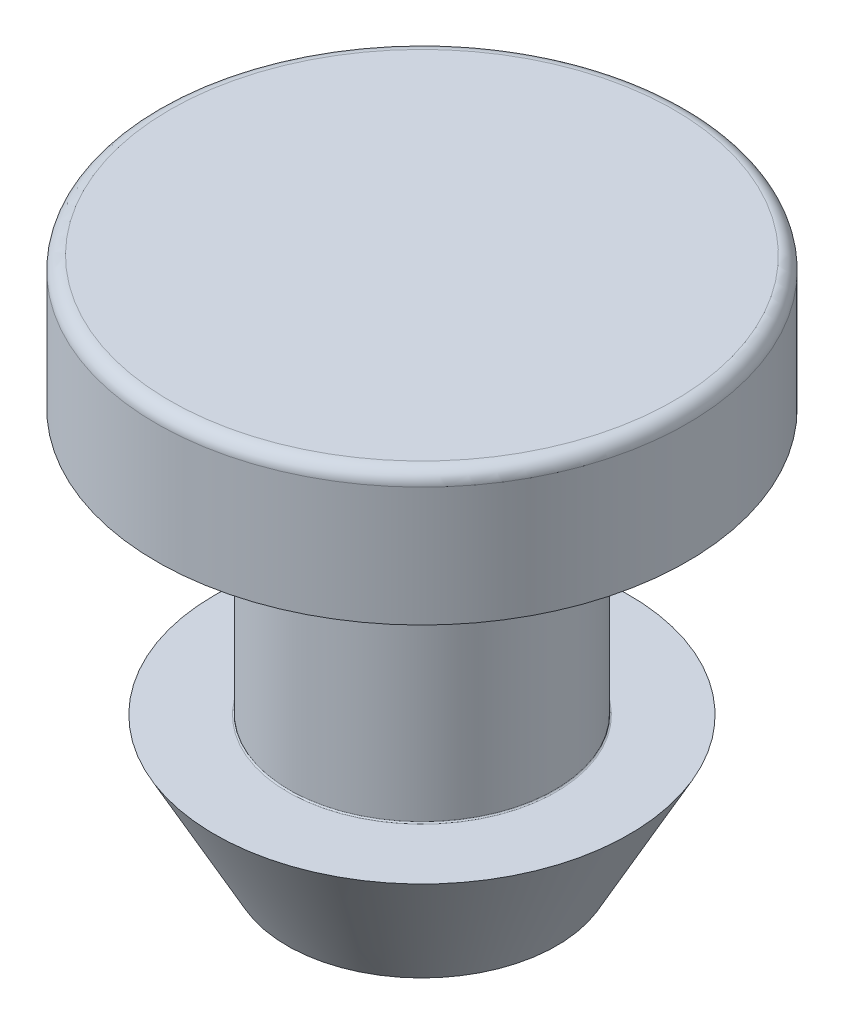
SolidWorks part; units mm, degrees
material "SBR"
ref_plane "Front Plane" through (0, 0, 0) normal (0, 0, 1) x (1, 0, 0)
ref_plane "Top Plane" through (0, 0, 0) normal (0, 1, 0) x (1, 0, 0)
ref_plane "Right Plane" through (0, 0, 0) normal (1, 0, 0) x (0, 0, -1)
sketch "Sketch1" plane through (0, 0, 0) normal (0, 0, 1) x (1, 0, 0)
  line L0 (0, 0) -> (0, -6.35) construction
  line L1 (-3.175, 0) -> (3.175, 0) construction
  line L2 (0, 0) -> (0, 3.175) construction
  line L3 (-6.35, 3.175) -> (6.35, 3.175) construction
  line L4 (0, -6.35) -> (0, -9.525) construction
  line L5 (-4.9609, -6.35) -> (4.9609, -6.35) construction
  line L6 (-3.2246, -9.525) -> (3.2246, -9.525) construction
  line L7 (-3.175, 0) -> (-3.175, -6.35) construction
  line L8 (3.175, 0) -> (3.175, -6.35) construction
  point P8 (0, 0)
  point P11 (0, -6.35)
  point P14 (0, -6.35)
  point P15 (6.35, 0)
  point P20 (-6.35, 0)
  dimension "Height" = 3.175
  dimension "OD" = 12.7
  dimension "For ID" = 6.35
  dimension "Ridge Diameter" = 9.9219
  dimension "Est Tip OD" = 6.4492
  dimension "Overall Height" = 12.7
  dimension "For Material Thickness" = 6.35
sketch "Sketch2" plane through (0, 0, 0) normal (0, 0, 1) x (1, 0, 0)
  line L0 (0, 3.175) -> (0, -9.525)
  line L7 (6.0325, 3.175) -> (0, 3.175)
  line L8 (0, -6.35) -> (0, -9.525) construction
  line L13 (6.35, 2.8575) -> (6.35, 0)
  line L14 (6.35, 0) -> (3.2067, 0)
  line L15 (3.175, -0.0318) -> (3.175, -6.3182)
  line L16 (-4.9609, -6.35) -> (4.9609, -6.35) construction
  line L17 (3.2068, -6.35) -> (4.9609, -6.35)
  line L18 (4.9609, -6.35) -> (3.2246, -9.525)
  line L19 (3.2246, -9.525) -> (0, -9.525)
  arc A0 (6.0325, 3.175) -> (6.35, 2.8575) centre (6.0325, 2.8575) cw
  arc A1 (3.175, -6.3182) -> (3.2068, -6.35) centre (3.2068, -6.3182) ccw
  arc A2 (3.2067, 0) -> (3.175, -0.0318) centre (3.2067, -0.0318) ccw
  point P13 (3.175, -6.35)
  point P21 (3.175, 0)
  dimension "D1" = 0.3175
  dimension "D2" = 0.0318
revolve "Revolve1" add sketch "Sketch2" angle 360 about L0
sketch "Sketch3" plane through (0, -9.525, 0) normal (0, -1, 0) x (1, 0, 0)
  line L0 (0, 0) -> (0, 2.282) construction
  circle A0 centre (0, 2.282) radius 0.3473
  circle A1 centre (1.9763, -1.141) radius 0.3473
  circle A2 centre (-1.9763, -1.141) radius 0.3473
  point P10 (0, 0)
  dimension "D1" = 0.6945
  dimension "D2" = 2.282
  dimension "D3" = 3
extrude "Cut-Extrude1" cut sketch "Sketch3" against normal blind 0.3175
equation "\"Est Tip OD@Sketch1\" = \"Ridge Diameter@Sketch1\" * .65"
equation "\"D1@Sketch2\"=\"OD@Sketch1\"*.025"
equation "\"D2@Sketch2\"=\"D1@Sketch2\"*.1"
equation "\"D1@Sketch3\" = \"Ridge Diameter@Sketch1\" * .07"
equation "\"D2@Sketch3\" = \"Ridge Diameter@Sketch1\" * .23"
equation "\"D1@Cut-Extrude1\" =  ( \"Overall Height@Sketch1\" - \"Height@Sketch1\" - \"For Material Thickness@Sketch1\" )  * .1"
